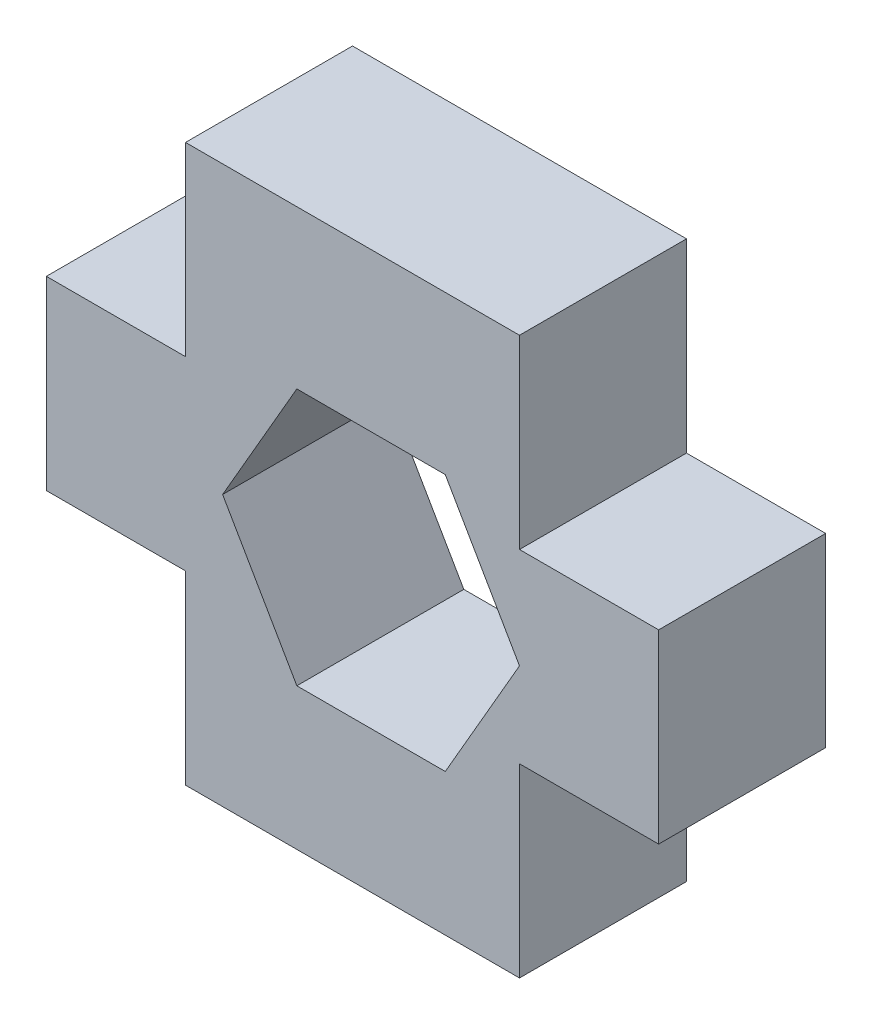
SolidWorks part; units mm, degrees
ref_plane "Front Plane" through (0, 0, 0) normal (0, 0, 1) x (1, 0, 0)
ref_plane "Top Plane" through (0, 0, 0) normal (0, 1, 0) x (1, 0, 0)
ref_plane "Right Plane" through (0, 0, 0) normal (1, 0, 0) x (0, 0, -1)
sketch "Sketch1" plane through (0, 0, 0) normal (0, 0, 1) x (1, 0, 0)
  line L0 (0, 0) -> (7.2, 0)
  line L1 (7.2, 0) -> (7.2, 4)
  line L2 (7.2, 4) -> (10.2, 4)
  line L3 (10.2, 4) -> (10.2, 8)
  line L4 (7.2, 8) -> (10.2, 8)
  line L5 (7.2, 8) -> (7.2, 12)
  line L6 (7.2, 12) -> (0, 12)
  line L7 (0, 12) -> (0, 8)
  line L8 (0, 8) -> (-3, 8)
  line L9 (-3, 8) -> (-3, 4)
  line L10 (-3, 4) -> (0, 4)
  line L11 (0, 4) -> (0, 0)
  line L14 (7.2, 5.8268) -> (5.6, 8.5981)
  line L15 (5.6, 8.5981) -> (2.4, 8.5981)
  line L16 (2.4, 8.5981) -> (0.8, 5.8268)
  line L17 (0.8, 5.8268) -> (2.4, 3.0555)
  line L18 (2.4, 3.0555) -> (5.6, 3.0555)
  line L19 (5.6, 3.0555) -> (7.2, 5.8268)
  dimension "D1" = 3
  dimension "D5" = 2.4
  dimension "D2" = 4
  dimension "D3" = 3.2
  dimension "D4" = 7.2
  dimension "D6" = 3.0555
  dimension "D7" = 5.8268
extrude "Boss-Extrude1" add sketch "Sketch1" along normal blind 3.6
sketch "Sketch2" [suppressed] plane through (-3, 0, 0) normal (-1, 0, 0) x (0, 0, 1)
  line L0 (2, 0) -> (2, 7) construction
  line L1 (4, 4) -> (4, 5) construction
  line L2 (4, 4) -> (5, 4) construction
  line L3 (0, 4) -> (-1, 4) construction
  line L4 (0, 4) -> (0, 5) construction
  line L5 (0, 6) -> (3.7, 6) construction
  line L6 (0, 8) -> (0, 4) construction
  line L7 (0, 8) -> (0, 7) construction
  line L8 (0, 8) -> (-1, 8) construction
  line L9 (4, 8) -> (5, 8) construction
  line L10 (4, 8) -> (4, 7) construction
  arc A0 (4, 5) -> (5, 4) centre (5, 5) ccw construction
  arc A1 (0, 5) -> (-1, 4) centre (-1, 5) cw construction
  arc A2 (0, 7) -> (-1, 8) centre (-1, 7) ccw construction
  arc A3 (4, 7) -> (5, 8) centre (5, 7) cw construction
  dimension "D1" = 1
  dimension "D2" = 1
  dimension "D3" = 4
  dimension "D4" = 4
  dimension "D6" = 4
sketch "Sketch3" plane through (0, 0, 3.6) normal (0, 0, 1) x (1, 0, 0)
  line L0 (2.4, 3.0555) -> (5.6, 8.5981) construction
  line L1 (2.4, 8.5981) -> (5.6, 3.0555) construction
  line L3 (2.4, 8.5981) -> (0.8, 5.8268)
  line L4 (0.8, 5.8268) -> (2.4, 3.0555)
  line L5 (2.4, 3.0555) -> (5.6, 3.0555)
  line L6 (5.6, 3.0555) -> (7.2, 5.8268)
  line L7 (7.2, 5.8268) -> (5.6, 8.5981)
  line L8 (5.6, 8.5981) -> (2.4, 8.5981)
  circle A0 centre (4, 5.8268) radius 2.7713 construction
extrude "Cut-Extrude1" [suppressed] cut sketch "Sketch3" against normal through all both and the other way through all
equation "\"D4@Sketch1\"= 8 - \"tol2@parametersSketch@prostheticParameters.SLDPRT\" * 2"
equation "\"D1@Boss-Extrude1\"=4 - \"tol2@parametersSketch@prostheticParameters.SLDPRT\""
